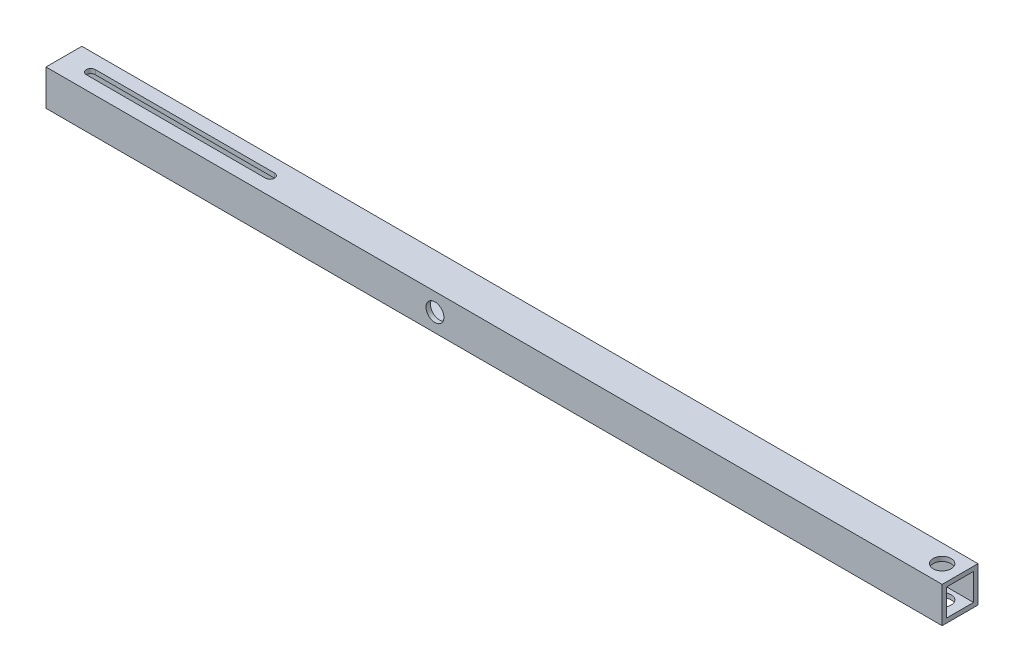
SolidWorks part; units mm, degrees
ref_plane "Front Plane" through (0, 0, 0) normal (0, 0, 1) x (1, 0, 0)
ref_plane "Top Plane" through (0, 0, 0) normal (0, 1, 0) x (1, 0, 0)
ref_plane "Right Plane" through (0, 0, 0) normal (1, 0, 0) x (0, 0, -1)
sketch "Sketch1" plane through (0, 0, 0) normal (0, 1, 0) x (1, 0, 0)
  line L1 (-250, -10) -> (250, -10)
  line L2 (-250, -10) -> (-250, 10)
  line L3 (-250, 10) -> (250, 10)
  line L4 (250, -10) -> (250, 10)
  line L5 (-250, -10) -> (250, 10) construction
  line L6 (-250, 10) -> (250, -10) construction
  point P0 (0, 0)
  dimension "D1" = 20
  dimension "D2" = 500
extrude "Boss-Extrude1" add sketch "Sketch1" along normal blind 20
sketch "Sketch4" plane through (250, 0, 0) normal (1, 0, 0) x (0, 0, -1)
  line L0 (-10, 0) -> (10, 0) construction
  circle A0 centre (0, 7.5) radius 5
  dimension "D2" = 10
  dimension "D1" = 7.5
extrude "Cut-Extrude3" [suppressed] cut sketch "Sketch4" against normal blind 50
sketch "Sketch5" plane through (-250, 0, 0) normal (-1, 0, 0) x (0, 0, 1)
  line L0 (-10, 0) -> (10, 0) construction
  circle A0 centre (0, 7.5) radius 5
  dimension "D2" = 10
  dimension "D1" = 7.5
extrude "Cut-Extrude4" [suppressed] cut sketch "Sketch5" against normal blind 50
sketch "Sketch6" plane through (0, 0, 10) normal (0, 0, 1) x (1, 0, 0)
  line L1 (-250, 0) -> (250, 0) construction
  line L2 (250, 20) -> (250, 0) construction
  circle A1 centre (-33, 10) radius 5
  dimension "D1" = 10
  dimension "D2" = 10
  dimension "D3" = 283
extrude "Cut-Extrude5" cut sketch "Sketch6" against normal through all
sketch "Sketch8" plane through (-250, 0, 0) normal (-1, 0, 0) x (0, 0, 1)
  line L0 (-10, 0) -> (10, 0) construction
  line L1 (-7.5, 2.5) -> (7.5, 2.5)
  line L2 (-7.5, 2.5) -> (-7.5, 17.5)
  line L3 (-7.5, 17.5) -> (7.5, 17.5)
  line L4 (7.5, 2.5) -> (7.5, 17.5)
  line L5 (-7.5, 2.5) -> (7.5, 17.5) construction
  line L6 (-7.5, 17.5) -> (7.5, 2.5) construction
  point P0 (0, 10)
  dimension "D1" = 10
  dimension "D2" = 15
  dimension "D3" = 15
extrude "Cut-Extrude7" cut sketch "Sketch8" against normal through all
sketch "Sketch9" plane through (0, 20, 0) normal (0, 1, 0) x (1, 0, 0)
  line L0 (-235, 0) -> (-135, 0) construction
  line L1 (-235, 2.5) -> (-135, 2.5)
  line L2 (-235, -2.5) -> (-135, -2.5)
  line L6 (-250, 10) -> (-250, -10) construction
  arc A0 (-235, 2.5) -> (-235, -2.5) centre (-235, 0) ccw
  arc A1 (-135, -2.5) -> (-135, 2.5) centre (-135, 0) ccw
  point P3 (-185, 0)
  dimension "D1" = 100
  dimension "D3" = 115
  dimension "D5" = 5
extrude "Cut-Extrude8" cut sketch "Sketch9" against normal blind 100
sketch "Sketch10" plane through (0, 20, 0) normal (0, 1, 0) x (1, 0, 0)
  line L0 (250, 10) -> (-250, 10) construction
  line L1 (250, -10) -> (250, 10) construction
  circle A0 centre (240, 0) radius 5
  dimension "D1" = 10
  dimension "D2" = 10
  dimension "D3" = 10
extrude "Cut-Extrude9" cut sketch "Sketch10" against normal through all
sketch "Sketch11" plane through (0, 0, -7.5) normal (0, 0, 1) x (1, 0, 0)
  line L1 (-250, 2.5) -> (-115.7478, 2.5)
  line L2 (-250, 2.5) -> (-250, 16.4021)
  line L3 (-250, 16.4021) -> (-115.7478, 16.4021)
  line L4 (-115.7478, 2.5) -> (-115.7478, 16.4021)
split line "Split Line1"
